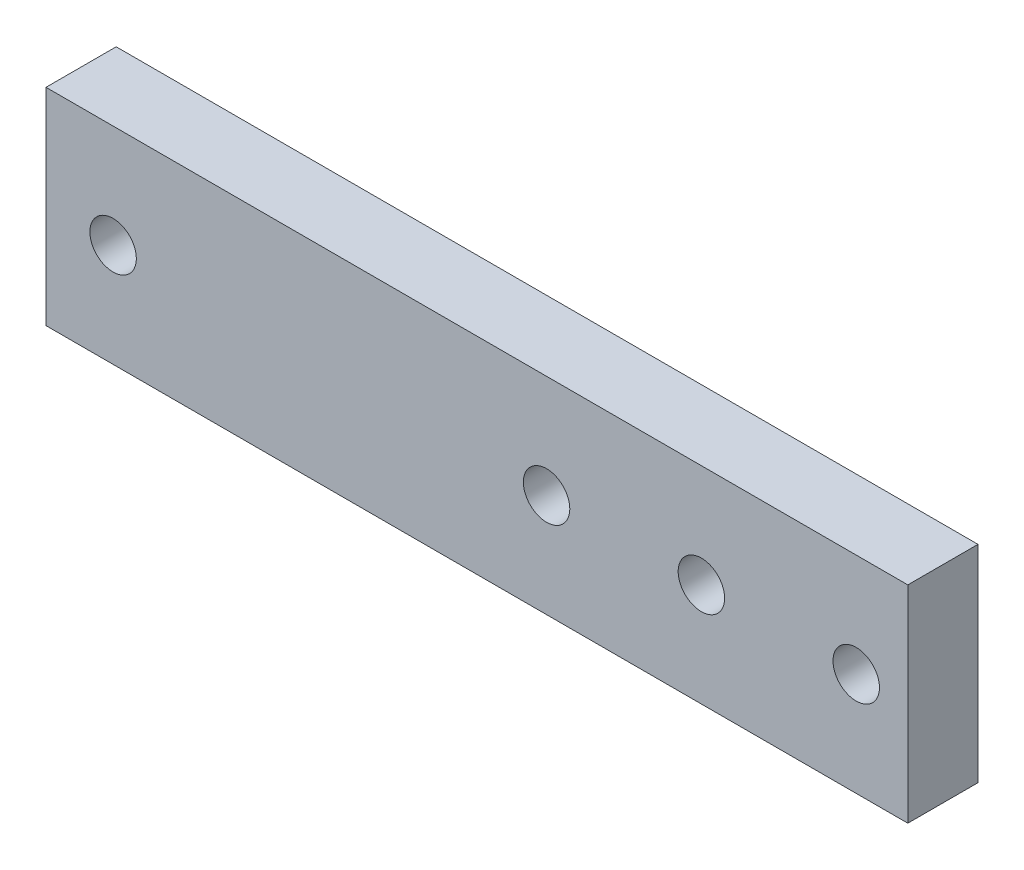
SolidWorks part; units mm, degrees
ref_plane "Front Plane" through (0, 0, 0) normal (0, 0, 1) x (1, 0, 0)
ref_plane "Top Plane" through (0, 0, 0) normal (0, 1, 0) x (1, 0, 0)
ref_plane "Right Plane" through (0, 0, 0) normal (1, 0, 0) x (0, 0, -1)
sketch "Sketch1" plane through (0, 0, 0) normal (0, 0, 1) x (1, 0, 0)
  line L0 (-14.25, 10) -> (-14.25, -10) construction
  line L1 (-41.75, -10) -> (41.75, -10)
  line L2 (-41.75, -10) -> (-41.75, 10)
  line L3 (-41.75, 10) -> (41.75, 10)
  line L4 (41.75, -10) -> (41.75, 10)
  line L5 (-41.75, -10) -> (41.75, 10) construction
  line L6 (-41.75, 10) -> (41.75, -10) construction
  circle A0 centre (6.75, 0) radius 2.25
  circle A1 centre (-35.25, 0) radius 2.25
  circle A2 centre (21.75, 0) radius 2.25
  circle A3 centre (36.75, 0) radius 2.25
  point P0 (0, 0)
  dimension "D1" = 42
  dimension "D2" = 4.5
  dimension "D4" = 15
  dimension "D5" = 15
  dimension "D6" = 6.5
  dimension "D7" = 5
  dimension "D3" = 20
extrude "Boss-Extrude1" add sketch "Sketch1" along normal blind 6.8
